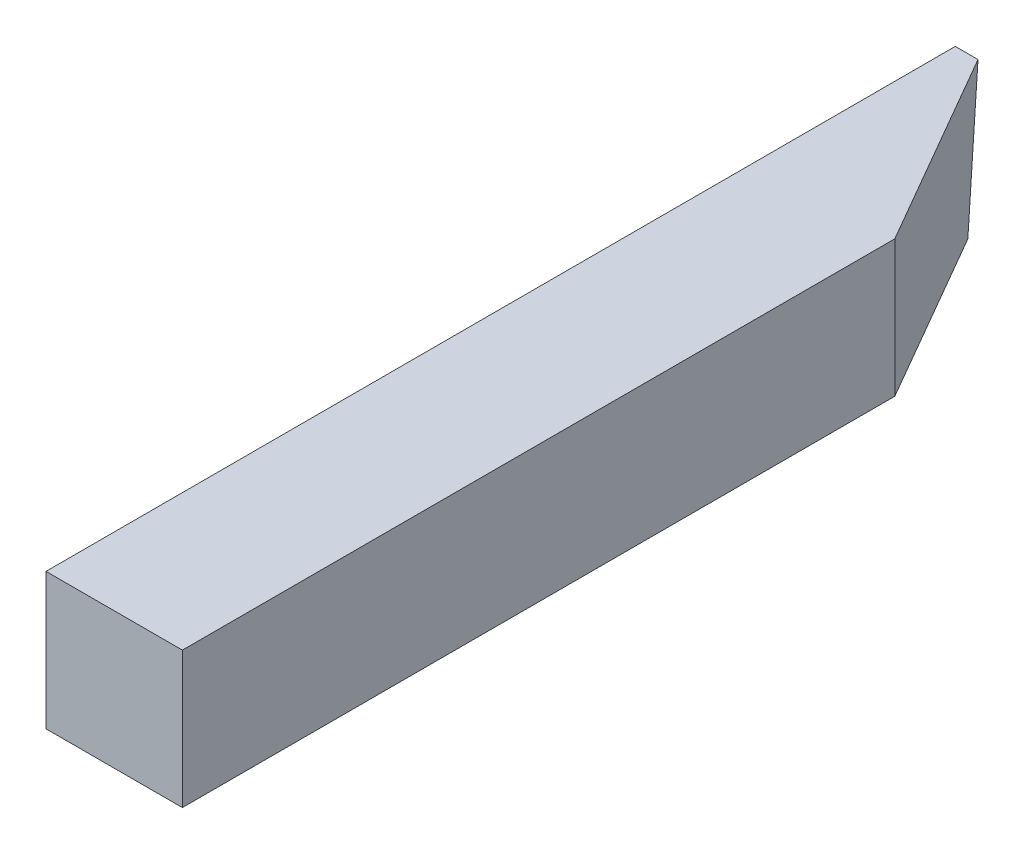
SolidWorks part; units mm, degrees
ref_plane "Front Plane" through (0, 0, 0) normal (0, 0, 1) x (1, 0, 0)
ref_plane "Top Plane" through (0, 0, 0) normal (0, 1, 0) x (1, 0, 0)
ref_plane "Right Plane" through (0, 0, 0) normal (1, 0, 0) x (0, 0, -1)
sketch "Sketch1" plane through (0, 0, 0) normal (0, 1, 0) x (1, 0, 0)
  line L0 (0, 0) -> (0, 49.7518)
  line L1 (0, 49.7518) -> (-7.9375, 63.5)
  line L2 (-7.9375, 63.5) -> (-9.525, 63.5)
  line L3 (-9.525, 63.5) -> (-9.525, 0)
  line L4 (-9.525, 0) -> (0, 0)
  dimension "D1" = 63.5
  dimension "D2" = 1.5875
  dimension "D3" = 60
  dimension "D4" = 9.525
extrude "Boss-Extrude1" add sketch "Sketch1" along normal blind 9.525
sketch "Sketch2" plane through (0, 0, 0) normal (1, 0, 0) x (0, 0, -1)
  line L0 (63.5, 9.525) -> (61.8205, 0)
  line L1 (49.7518, 0) -> (63.5, 0) construction
  line L2 (61.8205, 0) -> (63.5, 0)
  line L3 (63.5, 0) -> (63.5, 9.525)
  dimension "D1" = 10
extrude "Cut-Extrude1" cut sketch "Sketch2" against normal blind 9.525
equation "\"a\"=2.33786"
